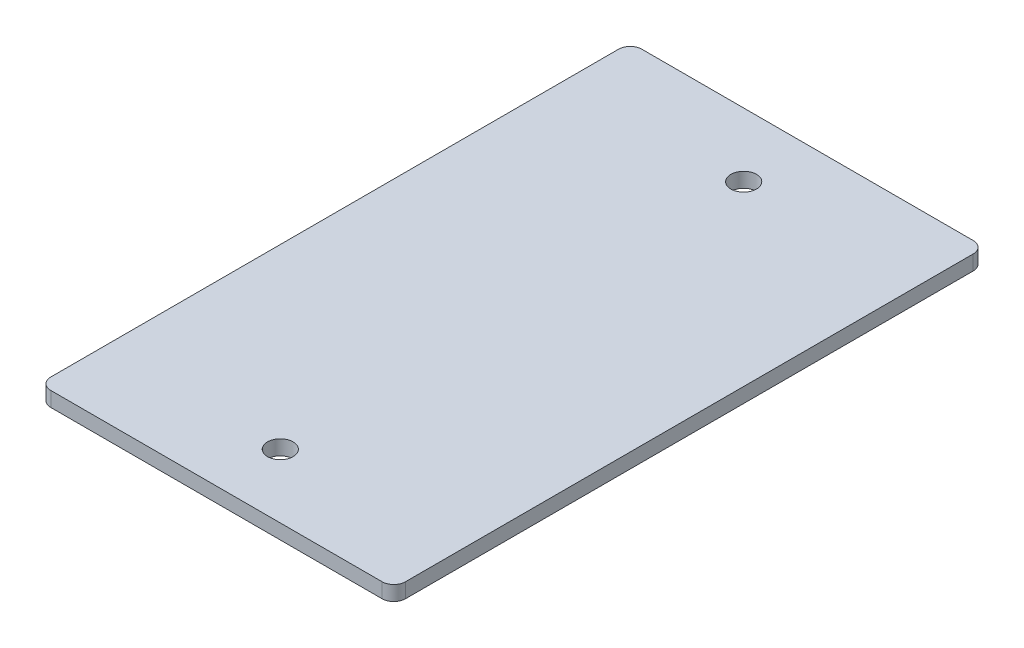
SolidWorks part; units mm, degrees
ref_plane "Front" through (0, 0, 0) normal (0, 0, 1) x (1, 0, 0)
ref_plane "Top" through (0, 0, 0) normal (0, 1, 0) x (1, 0, 0)
ref_plane "Right" through (0, 0, 0) normal (1, 0, 0) x (0, 0, -1)
sketch "Sketch1" plane through (0, 0, 0) normal (0, 1, 0) x (1, 0, 0)
  line L1 (-38.1, -63.5) -> (38.1, -63.5)
  line L2 (-38.1, -63.5) -> (-38.1, 63.5)
  line L3 (-38.1, 63.5) -> (38.1, 63.5)
  line L4 (38.1, -63.5) -> (38.1, 63.5)
  line L5 (-38.1, -63.5) -> (38.1, 63.5) construction
  line L6 (-38.1, 63.5) -> (38.1, -63.5) construction
  circle A0 centre (0, 49.785) radius 2.75
  circle A1 centre (0, -49.785) radius 2.75
  point P0 (0, 0)
  dimension "D1" = 5.5
  dimension "D2" = 5.5
  dimension "D3" = 99.57
  dimension "D4" = 127
  dimension "D5" = 76.2
  dimension "D6" = 49.785
extrude "Boss-Extrude1" add sketch "Sketch1" along normal blind 3.175
fillet "Fillet1" radius 2.5 4 edges at (38.1, 1.5875, -63.5) (-38.1, 1.5875, -63.5) (-38.1, 1.5875, 63.5) (38.1, 1.5875, 63.5)
equation "\"D6@Sketch1\"=\"D3@Sketch1\"/2"
